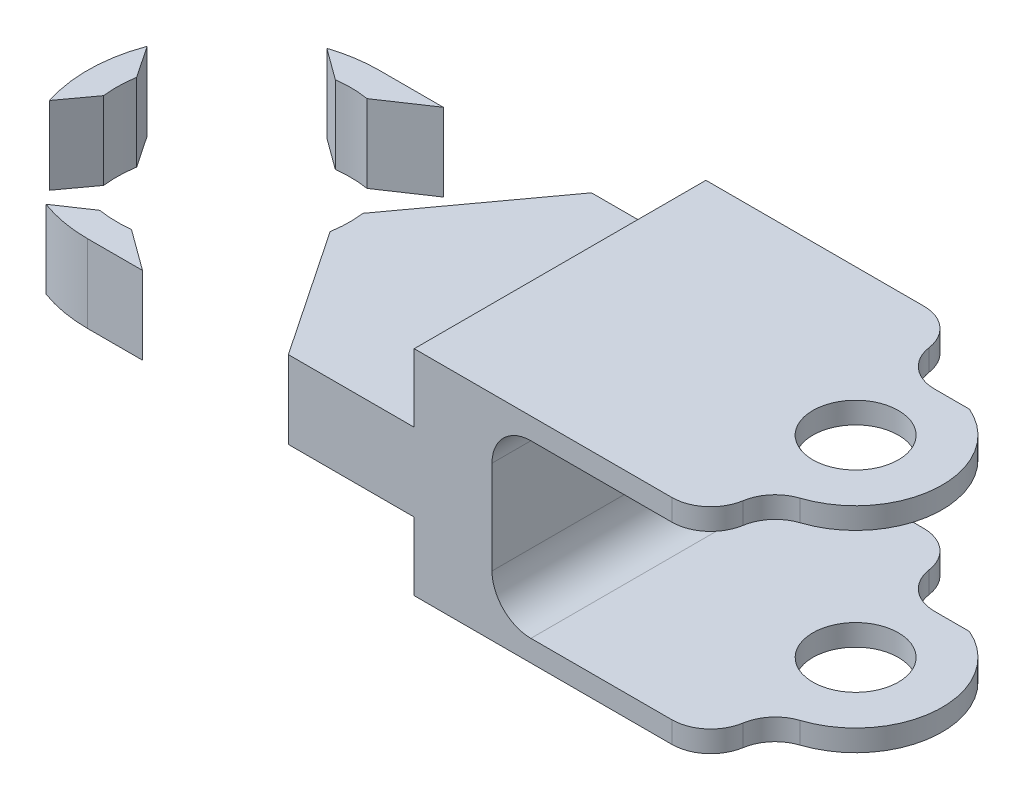
SolidWorks part; units mm, degrees
material "ABS"
ref_plane "Front Plane" through (0, 0, 0) normal (0, 0, 1) x (1, 0, 0)
ref_plane "Top Plane" through (0, 0, 0) normal (0, 1, 0) x (1, 0, 0)
ref_plane "Right Plane" through (0, 0, 0) normal (1, 0, 0) x (0, 0, -1)
sketch "Sketch1" plane through (0, 0, 0) normal (0, 1, 0) x (1, 0, 0)
  line L0 (0, 0) -> (40.64, 0) construction
  line L1 (0, 9.525) -> (40.64, 9.525)
  line L2 (0, -9.525) -> (40.64, -9.525)
  arc A0 (0, 9.525) -> (0, -9.525) centre (0, 0) ccw
  arc A1 (40.64, -9.525) -> (40.64, 9.525) centre (40.64, 0) ccw
  circle A2 centre (0, 0) radius 3.175
  circle A3 centre (40.64, 0) radius 2.794
  point P3 (20.32, 0)
  dimension "D2" = 5.588
  dimension "D4" = 6.35
  dimension "D1" = 40.64
  dimension "D3" = 19.05
extrude "Boss-Extrude1" add sketch "Sketch1" along normal blind 13.97
sketch "Sketch4" plane through (0, 0, 9.525) normal (0, 0, 1) x (1, 0, 0)
  line L0 (37.846, 0) -> (43.434, 0) construction
  line L1 (37.846, 0) -> (43.434, 0)
  line L2 (26.416, 0) -> (26.416, 13.97)
  line L3 (-997.5619, 6.985) -> (49002.4381, 6.985) construction
  line L4 (0, 0) -> (40.64, 0)
  line L5 (40.64, 0) -> (40.64, 13.97)
  line L6 (40.64, 13.97) -> (0, 13.97)
  line L7 (0, 13.97) -> (0, 0)
  line L8 (0, 0) -> (40.64, 0)
  line L9 (40.64, 0) -> (40.64, 13.97)
  line L10 (40.64, 13.97) -> (0, 13.97)
  line L11 (0, 13.97) -> (0, 0)
  line L12 (-978.7909, 1.397) -> (49021.2091, 1.397) construction
  line L13 (-979.2334, 12.573) -> (49020.7666, 12.573) construction
  line L14 (-9.525, 0) -> (0, 0) construction
  line L15 (26.416, 1.397) -> (57.18, 1.397)
  line L16 (26.416, 1.397) -> (26.416, 12.573)
  line L17 (26.416, 12.573) -> (57.18, 12.573)
  line L18 (57.18, 1.397) -> (57.18, 12.573)
  line L19 (-9.525, 0) -> (0, 0)
  line L20 (-9.525, 0) -> (-9.525, 13.97)
  line L21 (21.336, 9.525) -> (21.336, 13.97)
  line L22 (21.336, 4.445) -> (-9.525, 4.445)
  line L23 (21.336, 4.445) -> (21.336, 9.525)
  line L24 (21.336, 9.525) -> (-9.525, 9.525)
  line L25 (-9.525, 4.445) -> (-9.525, 9.525)
  line L26 (21.336, 4.445) -> (-9.525, 9.525) construction
  line L27 (21.336, 9.525) -> (-9.525, 4.445) construction
  line L28 (21.336, 4.445) -> (21.336, 0)
  line L29 (0, 13.97) -> (-11.5786, 13.97)
  point P9 (26.416, 6.985)
  point P14 (26.416, 1.397)
  point P16 (26.416, 12.573)
  point P22 (5.9055, 6.985)
  line M9 (0, 0) -> (40.64, 0)
  line M12 (0, 13.97) -> (0, 0)
  dimension "D2" = 11.43
  dimension "D3" = 5.588
  dimension "D4" = 5.588
  dimension "D5" = 5.08
  dimension "D6" = 5.08
  dimension "D1" = 0
extrude "Cut-Extrude1" cut sketch "Sketch4" against normal through all contours L15 L18 L17 L9 | L17 L2 L15 L9 | L28 L22 L11 M9 | L11 L22 L20 L19 | L24 L21 L10 M12 | L29 L20 L24 M12
sketch "Sketch5" plane through (0, 0, 0) normal (0, -1, 0) x (-1, 0, 0)
  line L1 (-38.0585, 17.3663) -> (-57.4599, 17.3663)
  line L2 (-38.0585, 17.3663) -> (-38.0585, 5.1857)
  line L3 (-38.0585, 5.1857) -> (-57.4599, 5.1857)
  line L4 (-57.4599, 17.3663) -> (-57.4599, 5.1857)
  line L5 (-38.0585, 17.3663) -> (-57.4599, 5.1857) construction
  line L6 (-38.0585, 5.1857) -> (-57.4599, 17.3663) construction
  point P0 (-47.7592, 11.276)
extrude "Cut-Extrude2" cut sketch "Sketch5" against normal through all
sketch "Sketch6" plane through (0, 13.97, 0) normal (0, 1, 0) x (1, 0, 0)
  line L0 (40.64, -5.6515) -> (40.64, -9.525)
  line L1 (48.6296, 5.1857) -> (38.0585, 5.1857) construction
  line L2 (48.6296, 5.1857) -> (38.0585, 5.1857)
  circle A0 centre (40.64, 0) radius 2.794 construction
  circle A1 centre (40.64, 0) radius 2.794
  circle A2 centre (40.64, 0) radius 5.6515
  arc A3 (40.64, -9.525) -> (48.6296, 5.1857) centre (40.64, 0) ccw construction
  arc A4 (40.64, -9.525) -> (48.6296, 5.1857) centre (40.64, 0) ccw
  arc M5 (40.64, -9.525) -> (48.6296, 5.1857) centre (40.64, 0) ccw
  line M6 (48.6296, 5.1857) -> (38.0585, 5.1857)
  dimension "D1" = 2.8575
extrude "Cut-Extrude3" cut sketch "Sketch6" against normal through all contours A2 L0 M5 M6
fillet "Fillet1" radius 2.54 1 edges at (40.64, 13.2715, 5.6515)
fillet "Fillet2" radius 2.54 1 edges at (40.64, 13.2715, 9.525)
fillet "Fillet3" radius 2.54 1 edges at (40.64, 0.6985, 5.6515)
fillet "Fillet4" radius 2.54 1 edges at (40.64, 0.6985, 9.525)
fillet "Fillet5" radius 2.54 2 edges at (38.0585, 0.6985, -5.1857) (38.0585, 13.2715, -5.1857)
fillet "Fillet6" radius 2.54 2 edges at (38.0585, 0.6985, -9.525) (38.0585, 13.2715, -9.525)
sketch3d "3DSketch2" plane through (0, 0, 0) normal (0, 0, 1) x (1, 0, 0)
  dimension "D1" = 5.588
sketch "Sketch7" plane through (0, 4.445, 0) normal (0, -1, 0) x (1, 0, 0)
  line L0 (-2.5005, 8.3939) -> (-11.2169, 14.2544) construction
  line L1 (-2.5005, 8.3939) -> (-11.2169, 14.2544)
  line L2 (2.1684, 8.4857) -> (10.6475, 14.6846) construction
  line L3 (0, -9.525) -> (21.336, -9.525)
  line L4 (21.336, -9.525) -> (21.336, 9.525)
  line L5 (21.336, 9.525) -> (0, 9.525)
  line L6 (0, -9.525) -> (21.336, -9.525)
  line L7 (21.336, -9.525) -> (21.336, 9.525)
  line L8 (21.336, 9.525) -> (0, 9.525)
  line L9 (-8.4857, 2.1684) -> (-14.6846, 10.6475) construction
  line L10 (2.1684, 8.4857) -> (10.6475, 14.6846)
  line L11 (-8.4857, 2.1684) -> (-14.6846, 10.6475)
  line L12 (2.5005, -8.3939) -> (11.2169, -14.2544) construction
  line L13 (8.4857, -2.1684) -> (14.6846, -10.6475) construction
  line L14 (2.5005, -8.3939) -> (11.2169, -14.2544)
  line L15 (8.4857, -2.1684) -> (14.6846, -10.6475)
  line L16 (-8.3939, -2.5005) -> (-14.2544, -11.2169) construction
  line L17 (-2.1684, -8.4857) -> (-10.6475, -14.6846) construction
  line L18 (-8.3939, -2.5005) -> (-14.2544, -11.2169)
  line L19 (-2.1684, -8.4857) -> (-10.6475, -14.6846)
  line L20 (8.3939, 2.5005) -> (14.2544, 11.2169) construction
  line L21 (8.3939, 2.5005) -> (14.2544, 11.2169)
  line L22 (2.1684, 8.4857) -> (0.9096, 7.5655)
  line L23 (-2.5005, 8.3939) -> (-1.2065, 7.5239)
  line L24 (-8.4857, 2.1684) -> (-7.5655, 0.9096)
  line L25 (-8.3939, -2.5005) -> (-7.5239, -1.2065)
  line L26 (-2.1684, -8.4857) -> (-0.9096, -7.5655)
  line L27 (2.5005, -8.3939) -> (1.2065, -7.5239)
  line L28 (8.4857, -2.1684) -> (7.5655, -0.9096)
  line L29 (8.3939, 2.5005) -> (7.5239, 1.2065)
  circle A0 centre (0, 0) radius 4.572
  arc A1 (0, 9.525) -> (0, -9.525) centre (0, 0) ccw
  arc A2 (0, 9.525) -> (0, -9.525) centre (0, 0) ccw
  circle A3 centre (0, 0) radius 7.62
  circle M7 centre (0, 0) radius 3.175
  arc M8 (0, 9.525) -> (0, -9.525) centre (0, 0) ccw
  dimension "D2" = 9.144
  dimension "D3" = 15.24
  dimension "D1" = 0
extrude "Cut-Extrude4" cut sketch "Sketch7" against normal blind 5.08 contours A3 A0 | A0 M7 | A3 L29 L21 L8 L10 L22 | A3 L27 L14 L6 L15 L28 | A3 L25 L18 L19 L26 M8 | A3 L23 L1 L11 L24 M8
fillet "Fillet7" radius 2.54 1 edges at (26.416, 12.573, 0)
fillet "Fillet8" radius 2.54 1 edges at (26.416, 1.397, 0)
